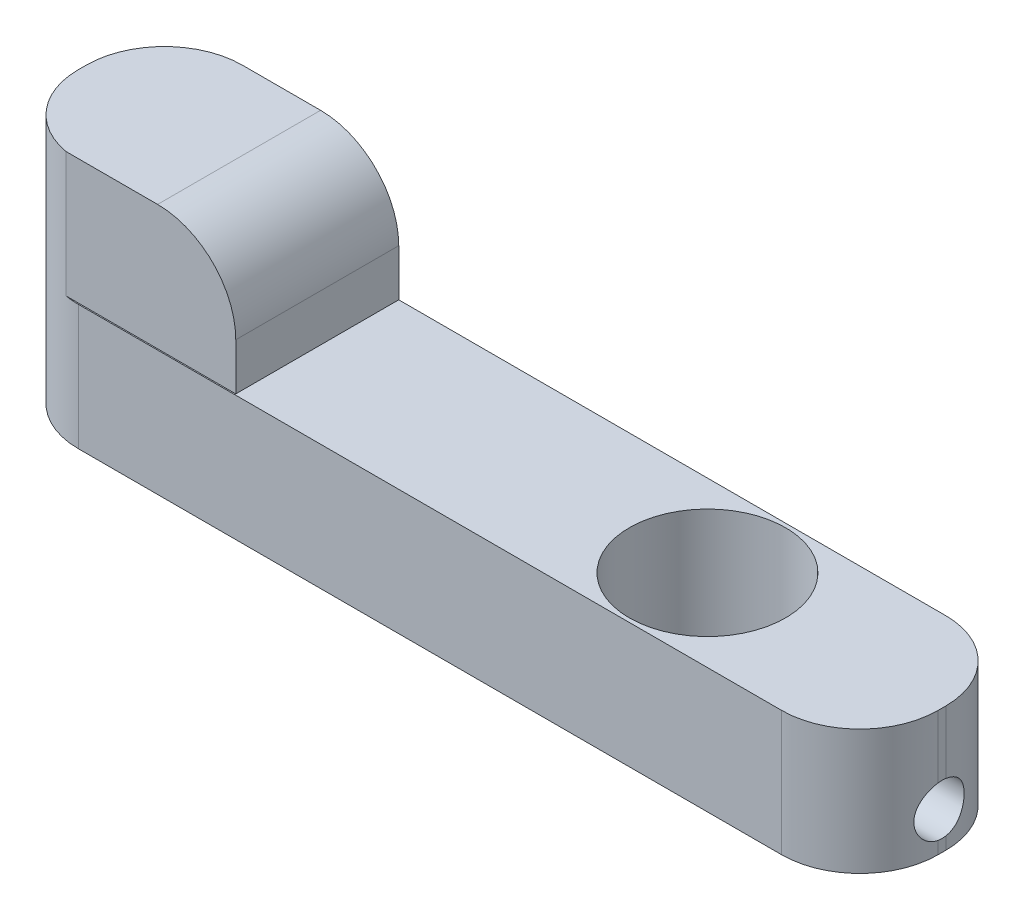
SolidWorks part; units mm, degrees
ref_plane "Front Plane" through (0, 0, 0) normal (0, 0, 1) x (1, 0, 0)
ref_plane "Top Plane" through (0, 0, 0) normal (0, 1, 0) x (1, 0, 0)
ref_plane "Right Plane" through (0, 0, 0) normal (1, 0, 0) x (0, 0, -1)
sketch "Sketch1" plane through (0, 0, 0) normal (0, 1, 0) x (1, 0, 0)
  line L0 (0, 0) -> (-275, 0) construction
  line L1 (-275, 52.5) -> (275, 52.5)
  line L2 (-275, 52.5) -> (-275, -52.5)
  line L3 (-275, -52.5) -> (275, -52.5)
  line L4 (275, 52.5) -> (275, -52.5)
  line L5 (-275, 52.5) -> (275, -52.5) construction
  line L6 (-275, -52.5) -> (275, 52.5) construction
  line L7 (0, 0) -> (275, 0) construction
  circle A0 centre (-220, 0) radius 50
  circle A1 centre (125, 0) radius 50
  point P0 (0, 0)
  dimension "D4" = 100
  dimension "D6" = 100
  dimension "D1" = 550
  dimension "D2" = 105
  dimension "D3" = 55
  dimension "D5" = 150
extrude "Boss-Extrude2" add sketch "Sketch1" along normal blind 80
fillet "Fillet4" radius 50 1 edges at (275, 40, 52.5)
fillet "Fillet5" radius 50 1 edges at (275, 40, -52.5)
sketch "Sketch11" plane through (0, 80, 0) normal (0, 1, 0) x (1, 0, 0)
  line L0 (-275, 52.5) -> (-125, 52.5)
  line L1 (-275, 52.5) -> (-275, -51.7681)
  line L2 (-125, 52.5) -> (-125, -51.7681)
  line L3 (-275, -51.7681) -> (-125, -51.7681)
  line L4 (225, 52.5) -> (-275, 52.5) construction
  dimension "D1" = 150
extrude "Boss-Extrude3" add sketch "Sketch11" along normal blind 80
sketch "Sketch12" plane through (0, 80, 0) normal (0, -1, 0) x (1, 0, 0)
  circle A0 centre (-220, 0) radius 5
  dimension "D1" = 10
extrude "Boss-Extrude4" add sketch "Sketch12" along normal blind 120
fillet "Fillet8" radius 50 3 edges at (-275, 80, 52.1341) (-275, 120, 51.7681) (-275, 40, 52.5)
fillet "Fillet9" radius 50 1 edges at (-275, 80, -52.5)
fillet "Fillet10" radius 50 1 edges at (-125, 160, -0.3659)
sketch "Sketch13" plane through (275, 0, 0) normal (1, 0, 0) x (0, 0, -1)
  line L0 (-51.7681, 80) -> (52.5, 80) construction
  circle A0 centre (0, 23.9) radius 16.1
  point P4 (0.3659, 80)
  dimension "D1" = 32.2
  dimension "D2" = 56.1
extrude "Cut-Extrude1" cut sketch "Sketch13" against normal blind 150 contours A0
